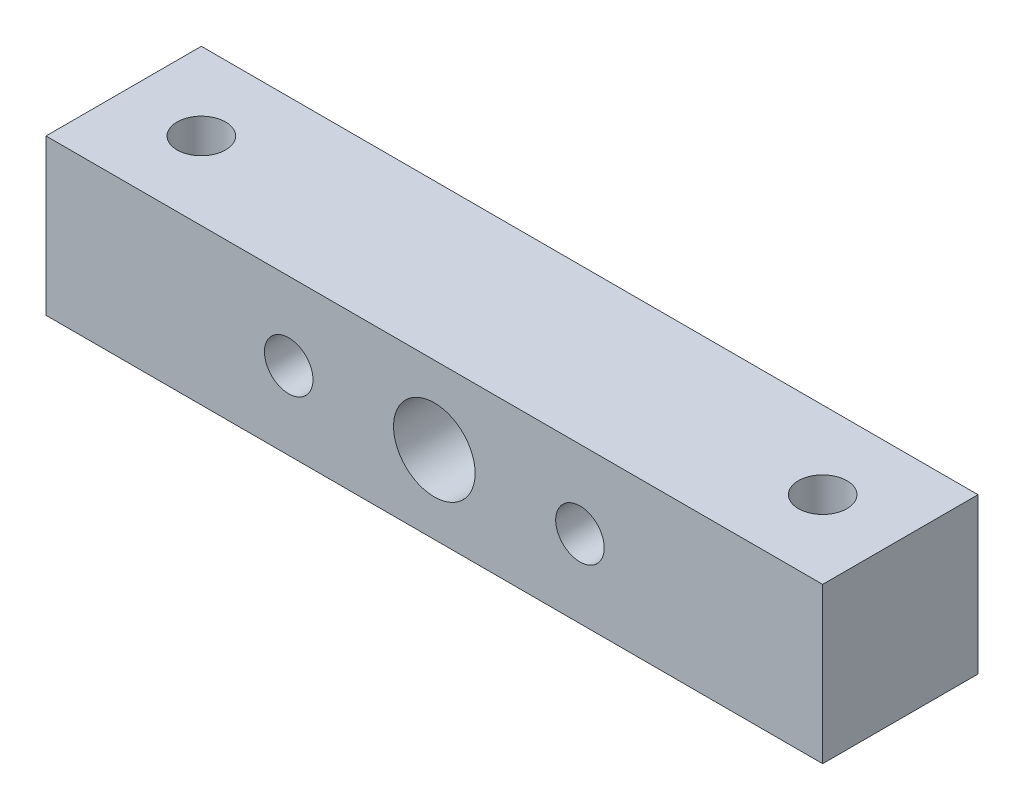
SolidWorks part; units mm, degrees
ref_plane "Front Plane" through (0, 0, 0) normal (0, 0, 1) x (1, 0, 0)
ref_plane "Top Plane" through (0, 0, 0) normal (0, 1, 0) x (1, 0, 0)
ref_plane "Right Plane" through (0, 0, 0) normal (1, 0, 0) x (0, 0, -1)
sketch "Sketch1" plane through (0, 0, 0) normal (0, 0, 1) x (1, 0, 0)
  line L0 (-7.5, 0) -> (7.5, 0) construction
  line L2 (20, -4) -> (-20, -4)
  line L3 (20, -4) -> (20, 4)
  line L4 (20, 4) -> (-20, 4)
  line L5 (-20, -4) -> (-20, 4)
  line L6 (20, -4) -> (-20, 4) construction
  line L7 (20, 4) -> (-20, -4) construction
  circle A0 centre (0, 0) radius 2.1
  circle A1 centre (7.5, 0) radius 1.25
  circle A2 centre (-7.5, 0) radius 1.25
  dimension "D2" = 4.2
  dimension "D3" = 2.5
  dimension "D1" = 15
  dimension "D4" = 8
  dimension "D5" = 40
extrude "Boss-Extrude1" add sketch "Sketch1" along normal blind 8
sketch "Sketch2" plane through (0, -4, 0) normal (0, -1, 0) x (1, 0, 0)
  line L0 (-16, 4) -> (16, 4) construction
  line L1 (0, 0) -> (0, 8) construction
  line L2 (-20, 0) -> (20, 0) construction
  line L3 (-20, 8) -> (20, 8) construction
  circle A0 centre (-16, 4) radius 1.25
  circle A1 centre (16, 4) radius 1.25
  point P6 (0, 4)
  dimension "D2" = 2.5
  dimension "D1" = 32
extrude "Cut-Extrude1" cut sketch "Sketch2" against normal through all
